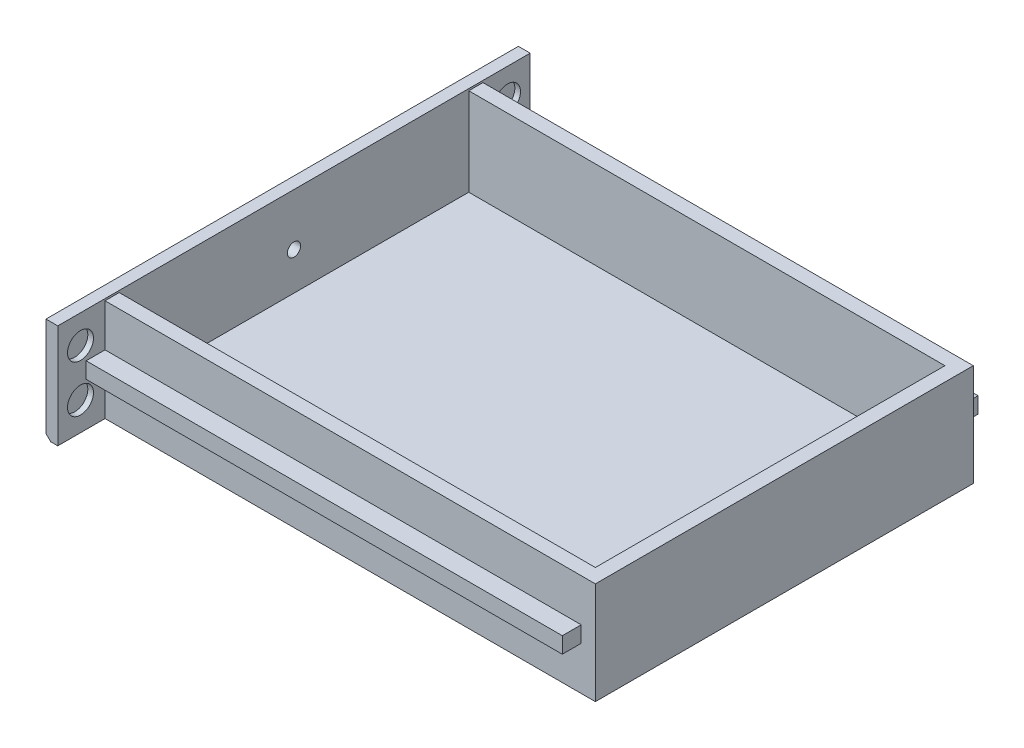
SolidWorks part; units mm, degrees
material "PLA"
ref_plane "Alzado" through (0, 0, 0) normal (0, 0, 1) x (1, 0, 0)
ref_plane "Planta" through (0, 0, 0) normal (0, 1, 0) x (1, 0, 0)
ref_plane "Vista lateral" through (0, 0, 0) normal (1, 0, 0) x (0, 0, -1)
sketch "Croquis1" plane through (0, 0, 0) normal (1, 0, 0) x (0, 0, -1)
  line L1 (-50, -11) -> (50, -11)
  line L2 (-50, -11) -> (-50, 11)
  line L3 (-50, 11) -> (50, 11)
  line L4 (50, -11) -> (50, 11)
  line L5 (-50, -11) -> (50, 11) construction
  line L6 (-50, 11) -> (50, -11) construction
  point P0 (0, 0)
extrude "Saliente-Extruir1" add sketch "Croquis1" along normal blind 2.5
sketch "Croquis4" plane through (2.5, 0, 0) normal (1, 0, 0) x (0, 0, -1)
  line L0 (0, -11) -> (0, 0) construction
  line L1 (-50, -11) -> (50, -11) construction
  line L2 (0, 0) -> (45.2, 0) construction
  line L3 (45.2, -5) -> (45.2, 5) construction
  circle A0 centre (45.2, 5) radius 2.75
  circle A1 centre (45.2, -5) radius 2.75
  circle A2 centre (-45.2, 5) radius 2.75
  circle A3 centre (-45.2, -5) radius 2.75
  point P9 (45.2, 0)
extrude "Cortar-Extruir2" cut sketch "Croquis4" against normal blind 1.2
sketch "Croquis6" plane through (2.5, 0, 0) normal (1, 0, 0) x (0, 0, -1)
  line L0 (0, 0) -> (0, 50000) construction
  line L1 (-50, -11) -> (50, -11) construction
  line L2 (40, -11) -> (-40, -11) construction
  line L3 (-40, -11) -> (-40, -1.8) construction
  line L4 (-40, -1.8) -> (-44, -1.8) construction
  line L5 (-44, -1.8) -> (-44, 1.6) construction
  line L6 (-44, 1.6) -> (-40, 1.6) construction
  line L7 (-40, -11) -> (40, -11)
  line L8 (-40, 1.6) -> (-40, 10.6)
  line L9 (-40, 10.6) -> (-37, 10.6)
  line L10 (-40, 1.6) -> (-44, 1.6)
  line L11 (-44, 1.6) -> (-44, -1.8)
  line L12 (-44, -1.8) -> (-40, -1.8)
  line L13 (-40, -1.8) -> (-40, -11)
  line L14 (-37, 10.6) -> (-37, -8)
  line L15 (-37, -8) -> (37, -8)
  line L16 (44, 1.6) -> (40, 1.6) construction
  line L17 (44, -1.8) -> (44, 1.6) construction
  line L18 (40, -1.8) -> (44, -1.8) construction
  line L19 (40, -11) -> (40, -1.8) construction
  line L20 (37, 10.6) -> (37, -8)
  line L21 (40, -1.8) -> (40, -11)
  line L22 (44, -1.8) -> (40, -1.8)
  line L23 (44, 1.6) -> (44, -1.8)
  line L24 (40, 1.6) -> (44, 1.6)
  line L25 (40, 10.6) -> (37, 10.6)
  line L26 (40, 1.6) -> (40, 10.6)
  point P19 (0, -8)
  point P22 (0, -11)
  dimension "D1" = 9.2
  dimension "D2" = 3.4
extrude "Saliente-Extruir2" add sketch "Croquis6" along normal blind 100.8
sketch "Croquis7" plane through (103.3, 0, 0) normal (1, 0, 0) x (0, 0, -1)
  line L1 (-40, 10.6) -> (40, 10.6)
  line L2 (-40, 10.6) -> (-40, -11)
  line L3 (-40, -11) -> (40, -11)
  line L4 (40, 10.6) -> (40, -11)
extrude "Saliente-Extruir3" add sketch "Croquis7" along normal blind 3
sketch "Croquis8" plane through (0, 0, 0) normal (-1, 0, 0) x (0, 0, 1)
  circle A0 centre (0, 0) radius 1.4
  dimension "D1" = 2.8
extrude "Cortar-Extruir3" cut sketch "Croquis8" against normal blind 3
chamfer "Chaflán1" distance 1 angle 45 1 edges at (0, -11, 0)
